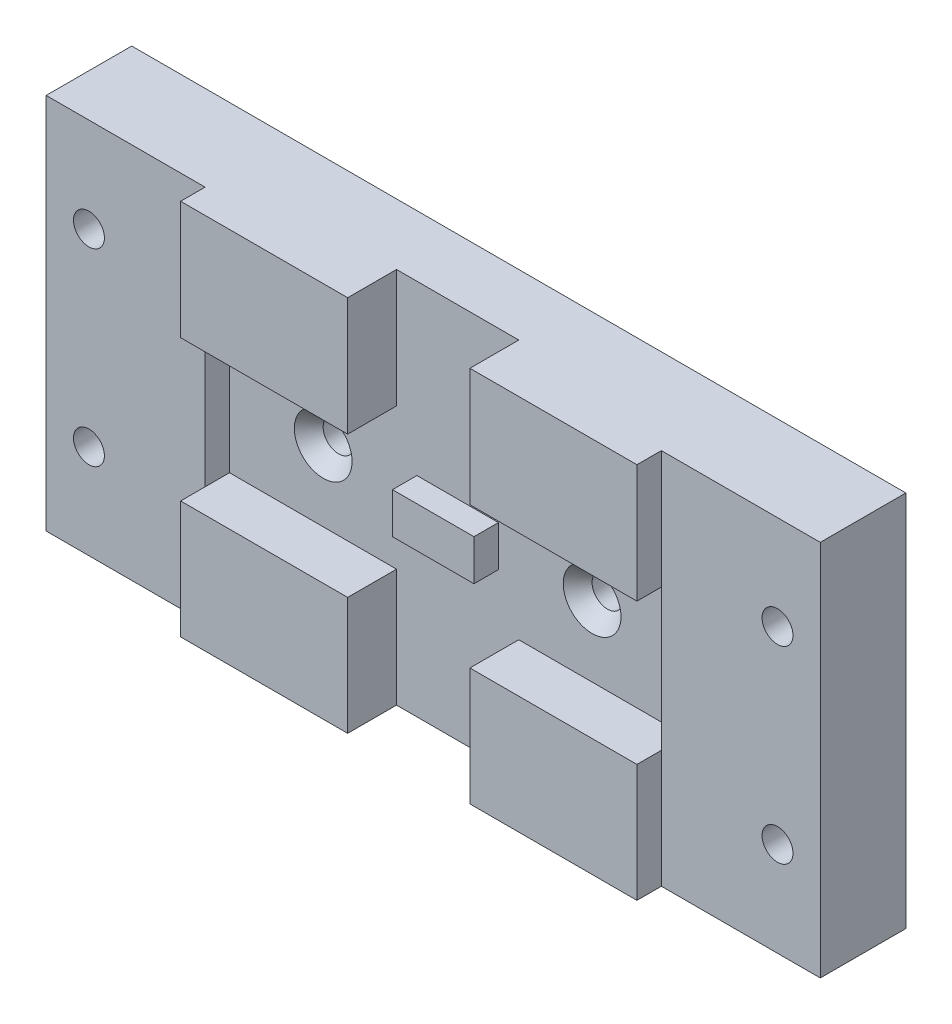
SolidWorks part; units mm, degrees
ref_plane "Front Plane" through (0, 0, 0) normal (0, 0, 1) x (1, 0, 0)
ref_plane "Top Plane" through (0, 0, 0) normal (0, 1, 0) x (1, 0, 0)
ref_plane "Right Plane" through (0, 0, 0) normal (1, 0, 0) x (0, 0, -1)
sketch "Reference Sketch" plane through (0, 0, 0) normal (0, 0, 1) x (1, 0, 0)
  line L0 (-40, -8.15) -> (-40, 8.15) construction
  line L1 (-40, -8.15) -> (40, -8.15) construction
  line L2 (-40, 8.15) -> (40, 8.15) construction
  line L3 (40, -8.15) -> (40, 8.15) construction
  line L4 (-40, -8.15) -> (40, 8.15) construction
  line L5 (-40, 8.15) -> (40, -8.15) construction
  line L6 (28, 8.15) -> (28, -8.15) construction
  line L7 (0, 8.15) -> (0, -8.15) construction
  line L8 (-28, 8.15) -> (-28, -8.15) construction
  line L9 (0, 8.15) -> (0, 15.65) construction
  line L10 (47.5, 23.15) -> (47.5, -23.15) construction
  line L11 (47.5, 0) -> (40, 0) construction
  line L12 (40, 0) -> (-40, 0) construction
  line L13 (-5, 2.5) -> (5, 2.5) construction
  line L14 (5, 2.5) -> (5, -2.5) construction
  line L15 (-5, -2.5) -> (5, -2.5) construction
  line L16 (-5, 2.5) -> (-5, -2.5) construction
  line L17 (47.5, 23.15) -> (-47.5, 23.15) construction
  line L18 (0, 15.65) -> (0, 23.15) construction
  line L19 (47.5, -23.15) -> (-47.5, -23.15) construction
  line L20 (0, -15.65) -> (0, -23.15) construction
  line L21 (0, -8.15) -> (0, -15.65) construction
  line L22 (-47.5, 23.15) -> (-47.5, -23.15) construction
  line L23 (37, 8.15) -> (37, -8.15) construction
  line L24 (-37, 8.15) -> (-37, -8.15) construction
  line L25 (37, 8.15) -> (47.5, 8.15) construction
  line L26 (42.25, 23.15) -> (42.25, -23.15) construction
  line L27 (-42.25, 23.15) -> (-42.25, -23.15) construction
  point P1 (0, 0)
  point P21 (5, 0)
  point P22 (0, -2.5)
  point P23 (0, 2.5)
  point P37 (42.25, 8.15)
  dimension "D1" = 16.3
  dimension "D2" = 80
  dimension "D3" = 12
  dimension "D4" = 10
  dimension "D5" = 5
  dimension "D6" = 7.5
  dimension "D7" = 3
sketch "Sketch2" plane through (0, 0, 0) normal (0, 0, 1) x (1, 0, 0)
  line L0 (-47.5, 23.15) -> (-47.5, -23.15)
  line L1 (-47.5, -23.15) -> (47.5, -23.15)
  line L2 (47.5, -23.15) -> (47.5, 23.15)
  line L3 (47.5, 23.15) -> (-47.5, 23.15)
extrude "Boss-Extrude1" add sketch "Sketch2" against normal blind 7.5
sketch "Sketch3" plane through (0, 0, 0) normal (0, 0, 1) x (1, 0, 0)
  line L0 (47.5, -23.15) -> (-47.5, -23.15) construction
  line L1 (5, 2.5) -> (-5, 2.5)
  line L2 (5, 2.5) -> (5, -2.5)
  line L3 (5, -2.5) -> (-5, -2.5)
  line L4 (-5, 2.5) -> (-5, -2.5)
  line L5 (47.5, 23.15) -> (28, 23.15)
  line L6 (47.5, 23.15) -> (47.5, -23.15)
  line L7 (47.5, -23.15) -> (28, -23.15)
  line L8 (28, 23.15) -> (28, -23.15)
  line L9 (28, 8.15) -> (28, -8.15) construction
  line L10 (-47.5, 23.15) -> (-28, 23.15)
  line L11 (-47.5, 23.15) -> (-47.5, -23.15)
  line L12 (-47.5, -23.15) -> (-28, -23.15)
  line L13 (-28, 23.15) -> (-28, -23.15)
  line L14 (-28, 8.15) -> (-28, -8.15) construction
extrude "Boss-Extrude2" add sketch "Sketch3" along normal blind 3
sketch "Sketch4" plane through (0, 0, 0) normal (0, 0, 1) x (1, 0, 0)
  line L15 (28, -8.15) -> (-28, -8.15)
  line L16 (28, -8.15) -> (28, -23.15)
  line L17 (28, -23.15) -> (-28, -23.15)
  line L18 (-28, -8.15) -> (-28, -23.15)
  line L20 (28, 23.15) -> (28, 8.15)
  line L34 (0, 0) -> (0, 23.15) construction
  line L36 (28, 23.15) -> (28, -23.15) construction
  line L37 (28, 8.15) -> (7.5, 8.15)
  line L39 (-40, 8.15) -> (40, -8.15) construction
  line L40 (7.5, 8.15) -> (7.5, 23.15)
  line L41 (47.5, 23.15) -> (-47.5, 23.15) construction
  line L42 (7.5, 23.15) -> (28, 23.15)
  line L43 (-40, 8.15) -> (40, 8.15) construction
  line L44 (-7.5, 23.15) -> (-28, 23.15)
  line L45 (-7.5, 8.15) -> (-7.5, 23.15)
  line L46 (-28, 8.15) -> (-7.5, 8.15)
  line L47 (-28, 23.15) -> (-28, 8.15)
  dimension "D1" = 15
extrude "Boss-Extrude3" add sketch "Sketch4" along normal blind 6
sketch "Sketch6" plane through (0, 0, 0) normal (0, 0, 1) x (1, 0, 0)
  line L0 (28, 0) -> (16.5, 0) construction
  line L3 (28, 8.15) -> (28, -8.15) construction
  line L4 (40, 0) -> (-40, 0) construction
  line L6 (16.5, 0) -> (5, 0) construction
  line L8 (0, 2.5) -> (0, -2.5) construction
  line L9 (-5, 2.5) -> (5, 2.5) construction
  line L10 (-16.5, 0) -> (-5, 0) construction
  line L11 (-28, 0) -> (-16.5, 0) construction
  point P16 (16.5, 0)
  point P19 (-16.5, 0)
hole_wizard "CSK for #6 Flat Head Machine Screw1" positions "Sketch9" profile "Sketch8" countersink size "#6" standard "ANSI Inch" end condition through all
sketch "Sketch9" plane through (0, 0, 0) normal (0, 0, 1) x (1, 0, 0)
  point P0 (16.5, 0)
  point P3 (-16.5, 0)
sketch "Sketch8" plane through (16.5, 0, 0) normal (1, 0, 0) x (0, -1, 0)
  line L0 (0, 0) -> (0, 7.5)
  line L1 (0, 7.5) -> (1.8986, 7.5)
  line L2 (1.8986, 7.5) -> (1.8986, 1.892)
  line L3 (1.8986, 1.892) -> (3.5433, 0)
  line L5 (3.5433, 0) -> (0, 0)
  line L6 (-1.8986, 1.892) -> (-3.5433, 0) construction
  line L11 (0, -6.35) -> (0, 107.95) construction
  dimension "Thru Hole Dia." = 3.7973
  dimension "Thru Hole Depth" = 7.5
  dimension "Near C'Sink Dia." = 7.0866
  dimension "Near C'Sink Angle" = 82
sketch "Sketch10" plane through (0, 0, -7.5) normal (0, 0, -1) x (-1, 0, 0)
  line L0 (42.25, 23.15) -> (42.25, 11.575) construction
  line L1 (42.25, 23.15) -> (42.25, -23.15) construction
  line L2 (42.25, 11.575) -> (42.25, 0) construction
  line L3 (42.25, 0) -> (42.25, -11.575) construction
  line L4 (42.25, -11.575) -> (42.25, -23.15) construction
  line L5 (-42.25, 23.15) -> (-42.25, 11.575) construction
  line L6 (-42.25, 23.15) -> (-42.25, -23.15) construction
  line L7 (-42.25, 11.575) -> (-42.25, 0) construction
  line L8 (-42.25, 0) -> (-42.25, -11.575) construction
  line L9 (-42.25, -11.575) -> (-42.25, -23.15) construction
  point P19 (-42.25, 11.575)
  point P20 (-42.25, -11.575)
  point P21 (42.25, 11.575)
  point P22 (42.25, -11.575)
hole_wizard "CSK for #6 Flat Head Machine Screw2" positions "Sketch11" profile "Sketch12" countersink size "#6" standard "ANSI Inch" end condition through all
sketch "Sketch11" plane through (0, 0, -7.5) normal (0, 0, -1) x (-1, 0, 0)
  point P0 (42.25, 11.575)
  point P3 (42.25, -11.575)
  point P6 (-42.25, 11.575)
  point P9 (-42.25, -11.575)
sketch "Sketch12" plane through (-42.25, 11.575, -7.5) normal (1, 0, 0) x (0, 1, 0)
  line L0 (0, 0) -> (0, 13.5)
  line L1 (0, 13.5) -> (1.8986, 13.5)
  line L2 (1.8986, 13.5) -> (1.8986, 1.892)
  line L3 (1.8986, 1.892) -> (3.5433, 0)
  line L5 (3.5433, 0) -> (0, 0)
  line L6 (-1.8986, 1.892) -> (-3.5433, 0) construction
  line L11 (0, -6.35) -> (0, 107.95) construction
  dimension "Thru Hole Dia." = 3.7973
  dimension "Thru Hole Depth" = 13.5
  dimension "Near C'Sink Dia." = 7.0866
  dimension "Near C'Sink Angle" = 82
sketch "Sketch18" plane through (0, 0, 0) normal (0, 0, 1) x (1, 0, 0)
  line L1 (-7.5, -32.0913) -> (7.5, -32.0913)
  line L2 (-7.5, -32.0913) -> (-7.5, -6.2824)
  line L3 (-7.5, -6.2824) -> (7.5, -6.2824)
  line L4 (7.5, -32.0913) -> (7.5, -6.2824)
extrude "Cut-Extrude4" cut sketch "Sketch18" along normal up to surface (6 mm away) up to face at (0, -15.65, 6)
sketch "Sketch19" plane through (0, 8.15, 0) normal (0, -1, 0) x (1, 0, 0)
  line L0 (28, 6) -> (28, 3) construction
  line L1 (-7.5, 0) -> (-28, 0)
  line L2 (-7.5, 0) -> (-7.5, 6)
  line L3 (-7.5, 6) -> (-28, 6)
  line L4 (-28, 0) -> (-28, 6)
  line L5 (7.5, 6) -> (28, 6)
  line L6 (7.5, 6) -> (7.5, 0)
  line L7 (7.5, 0) -> (28, 0)
  line L8 (28, 6) -> (28, 0)
  point P13 (0, 0)
extrude "Cut-Extrude5" cut sketch "Sketch19" against normal blind 0.5 and the other way blind 16.85
